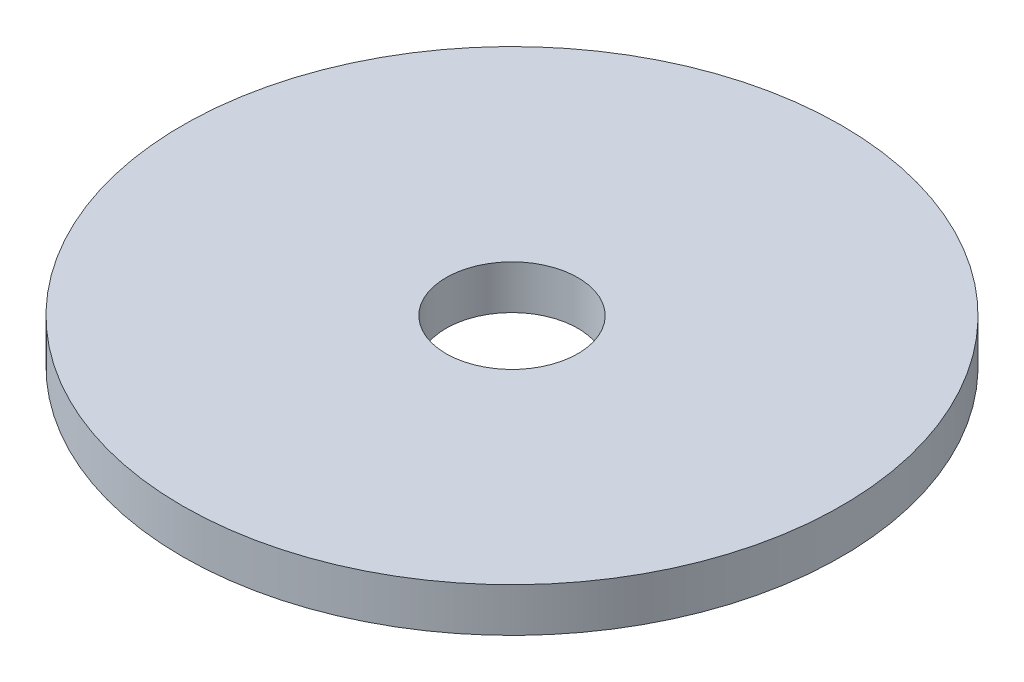
SolidWorks part; units mm, degrees
material "AISI 4130 Stal normalizowana w 870C"
ref_plane "Płaszczyzna XY" through (0, 0, 0) normal (0, 0, 1) x (1, 0, 0)
ref_plane "Płaszczyzna XZ" through (0, 0, 0) normal (0, 1, 0) x (1, 0, 0)
ref_plane "Płaszczyzna YZ" through (0, 0, 0) normal (1, 0, 0) x (0, 0, -1)
sketch "Szkic2" plane through (0, 0, 0) normal (0, 1, 0) x (1, 0, 0)
  circle A8 centre (0, 0) radius 15
  point P0 (0, 0)
  point P1 (0, 0)
  dimension "D1" = 30
  dimension "D2" = 0
extrude "Dodanie-wyciągnięcie1" add sketch "Szkic2" along normal blind 2
sketch "Szkic4" plane through (0, 2, 0) normal (0, 1, 0) x (1, 0, 0)
  circle A0 centre (0, 0) radius 3
  dimension "D1" = 6
  dimension "D3" = 0
extrude "Wytnij-wyciągnięcie1" cut sketch "Szkic4" against normal blind 10
